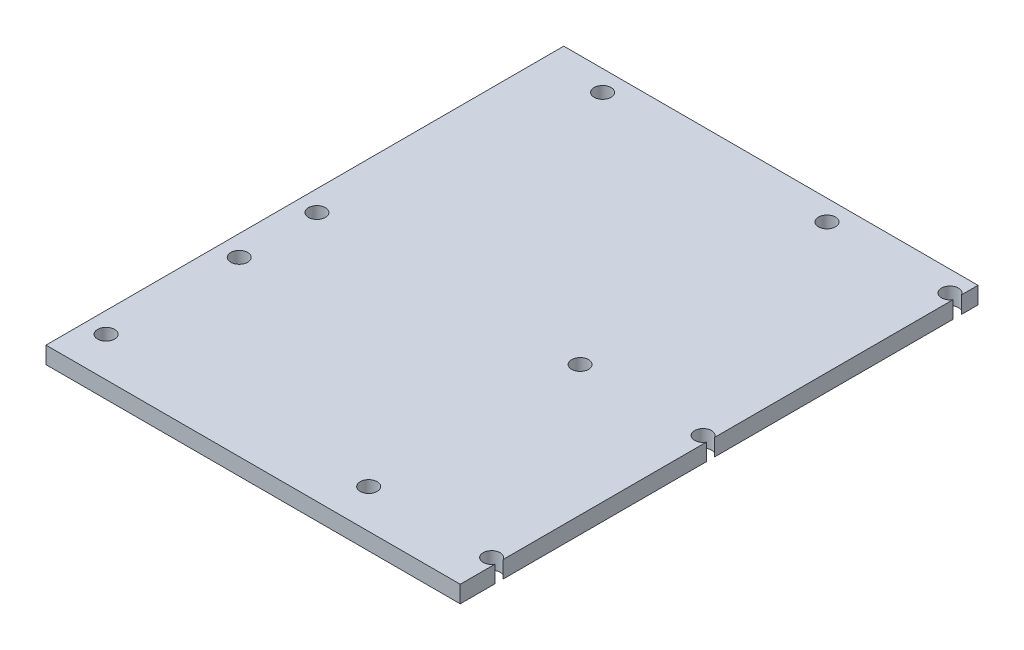
SolidWorks part; units mm, degrees
ref_plane "Front Plane" through (0, 0, 0) normal (0, 0, 1) x (1, 0, 0)
ref_plane "Top Plane" through (0, 0, 0) normal (0, 1, 0) x (1, 0, 0)
ref_plane "Right Plane" through (0, 0, 0) normal (1, 0, 0) x (0, 0, -1)
sketch "Sketch2" plane through (0, 0, 0) normal (0, 1, 0) x (1, 0, 0)
  line L1 (-121.92, -152.4) -> (121.92, -152.4)
  line L2 (-121.92, -152.4) -> (-121.92, 152.4)
  line L3 (-121.92, 152.4) -> (121.92, 152.4)
  line L4 (121.92, -152.4) -> (121.92, 152.4)
  line L5 (-121.92, -152.4) -> (121.92, 152.4) construction
  line L6 (-121.92, 152.4) -> (121.92, -152.4) construction
  point P0 (0, 0)
extrude "Boss-Extrude1" add sketch "Sketch2" along normal blind 10
sketch "Sketch1" plane through (0, 0, 0) normal (0, 1, 0) x (1, 0, 0)
  line L0 (-109.76, 152.4) -> (-109.76, -152.4) construction
  line L1 (-121.92, -152.4) -> (121.92, -152.4) construction
  line L2 (-121.92, -152.4) -> (-121.92, 152.4) construction
  line L3 (-121.92, 152.4) -> (121.92, 152.4) construction
  line L4 (121.92, -152.4) -> (121.92, 152.4) construction
  line L7 (-121.92, 140.24) -> (121.92, 140.24) construction
  line L8 (-121.92, -5.08) -> (121.92, -5.08) construction
  line L9 (-121.92, -50.8) -> (121.92, -50.8) construction
  line L10 (-121.92, -129.54) -> (121.92, -129.54) construction
  line L11 (45.18, 152.4) -> (45.18, -152.4) construction
  line L12 (117.57, 152.4) -> (117.57, -152.4) construction
  circle A0 centre (-86.9, 140.24) radius 5
  circle A1 centre (45.18, 140.24) radius 5
  circle A2 centre (117.57, 140.24) radius 5
  circle A3 centre (117.57, -5.08) radius 5
  circle A4 centre (45.18, -5.08) radius 5
  circle A5 centre (-109.76, -5.08) radius 5
  circle A6 centre (-109.76, -50.8) radius 5
  circle A7 centre (-109.76, -129.1961) radius 5
  circle A8 centre (45.18, -129.54) radius 5
  circle A9 centre (117.57, -129.54) radius 5
  point P0 (0, 0)
  point P40 (0, 0)
  dimension "D3" = 12.16
  dimension "D4" = 12.16
  dimension "D10" = 22.86
  dimension "D1" = 243.84
  dimension "D2" = 304.8
  dimension "D5" = 157.48
  dimension "D6" = 45.72
  dimension "D7" = 78.74
  dimension "D8" = 154.94
  dimension "D9" = 72.39
extrude "Cut-Extrude2" cut sketch "Sketch1" along normal up to surface (10 mm away) up to face at (0, 10, 0)
